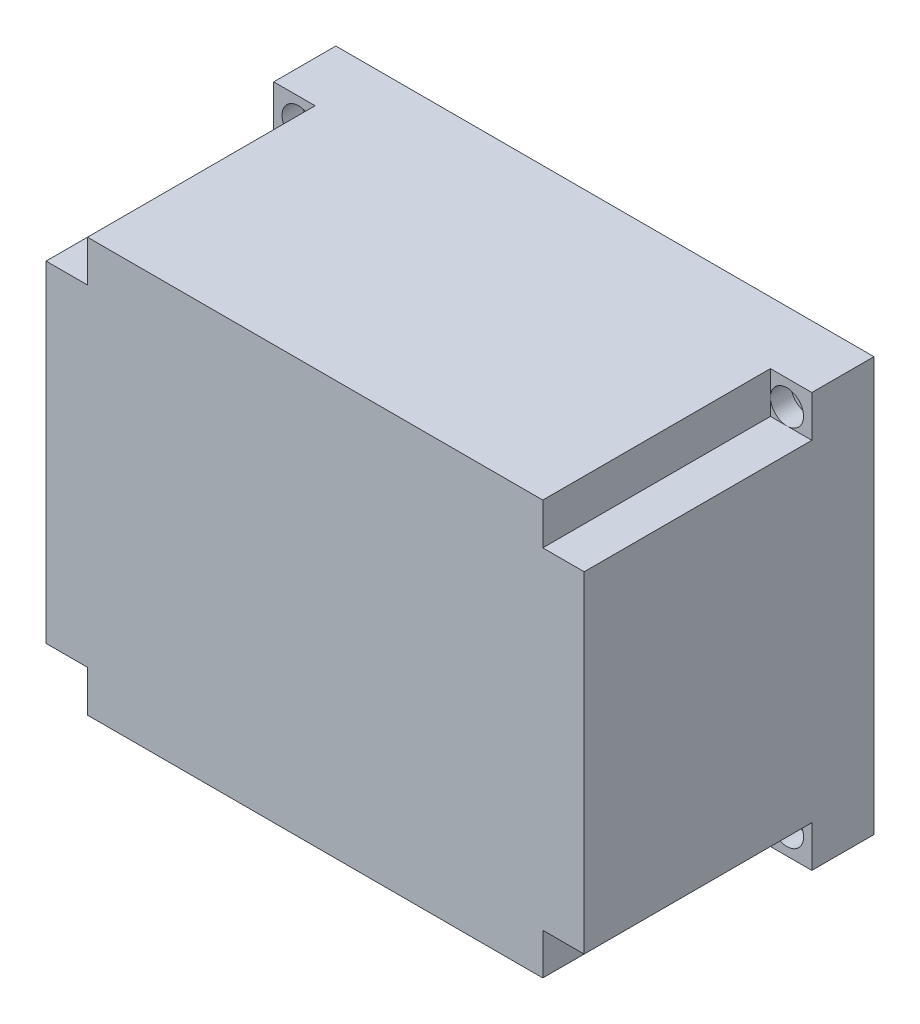
SolidWorks part; units mm, degrees
ref_plane "Front Plane" through (0, 0, 0) normal (0, 0, 1) x (1, 0, 0)
ref_plane "Top Plane" through (0, 0, 0) normal (0, 1, 0) x (1, 0, 0)
ref_plane "Right Plane" through (0, 0, 0) normal (1, 0, 0) x (0, 0, -1)
sketch "Sketch2" plane through (0, 0, 0) normal (0, 1, 0) x (1, 0, 0)
  line L1 (0, 0) -> (130, 0)
  line L2 (0, 0) -> (0, 70)
  line L3 (0, 70) -> (130, 70)
  line L4 (130, 0) -> (130, 70)
  dimension "D1" = 130
  dimension "D2" = 70
extrude "Boss-Extrude1" add sketch "Sketch2" along normal blind 100
sketch "Sketch3" plane through (0, 0, -70) normal (0, 0, -1) x (-1, 0, 0)
  line L0 (-130, 100) -> (0, 100) construction
  line L1 (-117, 87) -> (-13, 87)
  line L2 (-117, 87) -> (-117, 13)
  line L3 (-117, 13) -> (-13, 13)
  line L4 (-13, 87) -> (-13, 13)
  line L5 (-117, 87) -> (-13, 13) construction
  line L6 (-117, 13) -> (-13, 87) construction
  line L7 (-130, 100) -> (-130, 0) construction
  line L8 (-130, 0) -> (0, 0) construction
  line L9 (0, 100) -> (0, 0) construction
  point P0 (-65, 50)
  dimension "D1" = 13
  dimension "D2" = 13
  dimension "D3" = 13
  dimension "D4" = 13
extrude "Cut-Extrude1" cut sketch "Sketch3" against normal blind 67
sketch "Sketch4" plane through (0, 0, 0) normal (0, 0, 1) x (1, 0, 0)
  line L1 (0, 100) -> (10, 100)
  line L2 (0, 100) -> (0, 90)
  line L3 (0, 90) -> (10, 90)
  line L4 (10, 100) -> (10, 90)
  line L5 (130, 100) -> (120, 100)
  line L6 (130, 100) -> (130, 90)
  line L7 (130, 90) -> (120, 90)
  line L8 (120, 100) -> (120, 90)
  line L9 (0, 0) -> (10, 0)
  line L10 (0, 0) -> (0, 10)
  line L11 (0, 10) -> (10, 10)
  line L12 (10, 0) -> (10, 10)
  line L13 (130, 0) -> (120, 0)
  line L14 (130, 0) -> (130, 10)
  line L15 (130, 10) -> (120, 10)
  line L16 (120, 0) -> (120, 10)
  dimension "D1" = 10
  dimension "D2" = 10
  dimension "D3" = 10
  dimension "D4" = 10
  dimension "D5" = 10
  dimension "D6" = 10
  dimension "D7" = 10
  dimension "D8" = 10
extrude "Cut-Extrude2" cut sketch "Sketch4" against normal blind 55
sketch "Sketch5" plane through (0, 0, -70) normal (0, 0, -1) x (-1, 0, 0)
  line L0 (-130, 100) -> (0, 100) construction
  line L1 (-117, 87) -> (-13, 87)
  line L2 (-117, 87) -> (-117, 97)
  line L3 (-117, 97) -> (-13, 97)
  line L4 (-13, 87) -> (-13, 97)
  line L9 (-13, 13) -> (-117, 13)
  line L10 (-13, 13) -> (-13, 3)
  line L11 (-13, 3) -> (-117, 3)
  line L12 (-117, 13) -> (-117, 3)
  line L18 (-130, 0) -> (0, 0) construction
  dimension "D1" = 3
  dimension "D3" = 3
extrude "Cut-Extrude3" cut sketch "Sketch5" against normal blind 67
sketch "Sketch6" plane through (0, 0, -70) normal (0, 0, -1) x (-1, 0, 0)
  line L0 (-117, 97) -> (-117, 3) construction
  line L1 (-117, 87) -> (-127, 87)
  line L2 (-117, 87) -> (-117, 13)
  line L3 (-117, 13) -> (-127, 13)
  line L4 (-127, 87) -> (-127, 13)
  line L5 (-13, 3) -> (-13, 97) construction
  line L6 (-13, 87) -> (-3, 87)
  line L7 (-13, 87) -> (-13, 13)
  line L8 (-13, 13) -> (-3, 13)
  line L9 (-3, 87) -> (-3, 13)
  line L10 (-130, 100) -> (-130, 0) construction
  line L11 (-130, 100) -> (0, 100) construction
  line L12 (-130, 0) -> (0, 0) construction
  line L13 (0, 100) -> (0, 0) construction
  dimension "D1" = 3
  dimension "D2" = 13
  dimension "D3" = 13
  dimension "D4" = 13
  dimension "D5" = 3
  dimension "D6" = 13
extrude "Cut-Extrude4" cut sketch "Sketch6" against normal blind 67
sketch "Sketch9" plane through (0, 0, -70) normal (0, 0, -1) x (-1, 0, 0)
  line L0 (-130, 100) -> (0, 100) construction
  line L1 (-130, 100) -> (-130, 0) construction
  line L2 (0, 100) -> (0, 0) construction
  line L3 (-130, 0) -> (0, 0) construction
  circle A0 centre (-124, 94) radius 1.75
  circle A1 centre (-124, 6) radius 1.75
  circle A2 centre (-6, 94) radius 1.75
  circle A3 centre (-6, 6) radius 1.75
  point P4 (-107.3713, 88.8655)
  point P7 (-7.8416, 92)
  point P8 (-123.9805, 6.1022)
  point P11 (-7.8416, 6.1022)
  point P12 (-122.8257, 93.5015)
  dimension "D1" = 3.5
  dimension "D4" = 3.5
  dimension "D7" = 3.5
  dimension "D10" = 3.5
  dimension "D2" = 6
  dimension "D3" = 6
  dimension "D5" = 6
  dimension "D6" = 6
  dimension "D8" = 6
  dimension "D9" = 6
  dimension "D11" = 6
  dimension "D12" = 6
extrude "Cut-Extrude5" cut sketch "Sketch9" against normal blind 67
sketch "Sketch10" plane through (0, 0, -55) normal (0, 0, 1) x (1, 0, 0)
  line L0 (130, 100) -> (120, 100) construction
  line L1 (130, 90) -> (130, 100) construction
  circle A0 centre (124, 94) radius 4
  dimension "D3" = 8
  dimension "D1" = 6
  dimension "D2" = 6
extrude "Cut-Extrude6" cut sketch "Sketch10" against normal blind 5
sketch "Sketch12" plane through (0, 0, -55) normal (0, 0, 1) x (1, 0, 0)
  line L0 (130, 0) -> (130, 10) construction
  line L1 (120, 0) -> (130, 0) construction
  circle A0 centre (124, 6) radius 4
  dimension "D3" = 8
  dimension "D1" = 6
  dimension "D2" = 6
extrude "Cut-Extrude7" cut sketch "Sketch12" against normal blind 5
sketch "Sketch13" plane through (0, 0, -55) normal (0, 0, 1) x (1, 0, 0)
  line L0 (0, 0) -> (10, 0) construction
  line L1 (0, 10) -> (0, 0) construction
  circle A0 centre (6, 6) radius 4
  dimension "D3" = 8
  dimension "D1" = 6
  dimension "D2" = 6
extrude "Cut-Extrude8" cut sketch "Sketch13" against normal blind 5
sketch "Sketch14" plane through (0, 0, -55) normal (0, 0, 1) x (1, 0, 0)
  line L0 (0, 100) -> (0, 90) construction
  line L1 (10, 100) -> (0, 100) construction
  circle A0 centre (6, 94) radius 4
  dimension "D3" = 8
  dimension "D1" = 6
  dimension "D2" = 6
extrude "Cut-Extrude9" cut sketch "Sketch14" against normal blind 5
sketch "Sketch15" plane through (0, 0, -70) normal (0, 0, -1) x (-1, 0, 0)
  line L1 (-117, 87) -> (-120, 87)
  line L2 (-117, 87) -> (-117, 90)
  line L3 (-117, 90) -> (-120, 90)
  line L4 (-120, 87) -> (-120, 90)
  line L5 (-117, 13) -> (-120, 13)
  line L6 (-117, 13) -> (-117, 10)
  line L7 (-117, 10) -> (-120, 10)
  line L8 (-120, 13) -> (-120, 10)
  line L9 (-13, 13) -> (-10, 13)
  line L10 (-13, 13) -> (-13, 10)
  line L11 (-13, 10) -> (-10, 10)
  line L12 (-10, 13) -> (-10, 10)
  line L13 (-13, 87) -> (-10, 87)
  line L14 (-13, 87) -> (-13, 90)
  line L15 (-13, 90) -> (-10, 90)
  line L16 (-10, 87) -> (-10, 90)
  dimension "D1" = 3
  dimension "D2" = 3
  dimension "D3" = 3
  dimension "D4" = 3
  dimension "D5" = 3
  dimension "D6" = 3
  dimension "D7" = 3
  dimension "D8" = 3
extrude "Boss-Extrude2" add sketch "Sketch15" along normal blind 5
